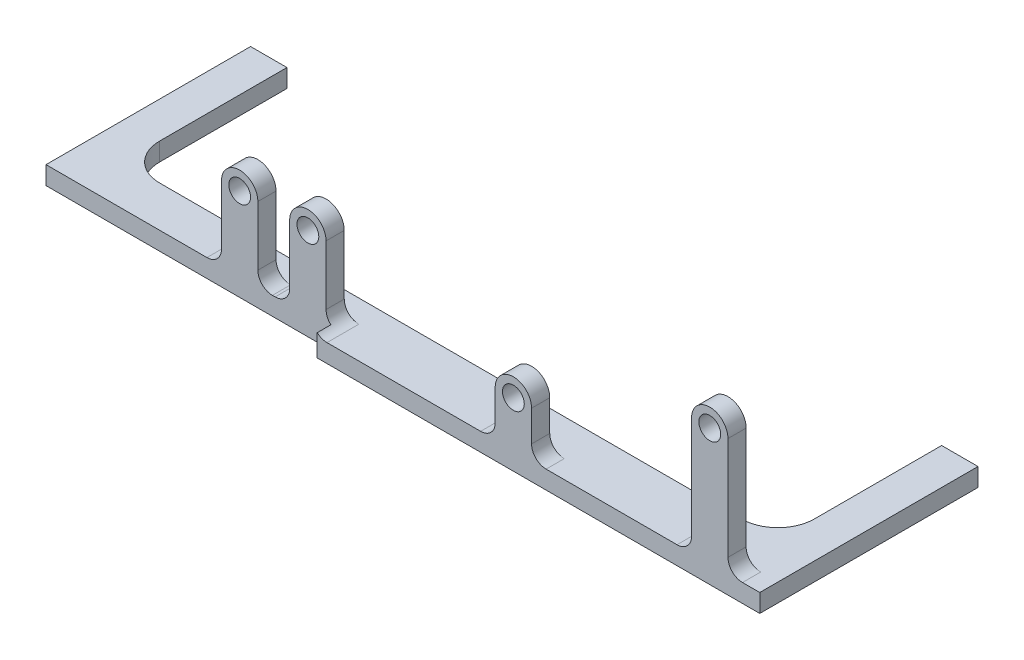
SolidWorks part; units mm, degrees
material "Alloy Steel"
ref_plane "Front Plane" through (0, 0, 0) normal (0, 0, 1) x (1, 0, 0)
ref_plane "Top Plane" through (0, 0, 0) normal (0, 1, 0) x (1, 0, 0)
ref_plane "Right Plane" through (0, 0, 0) normal (1, 0, 0) x (0, 0, -1)
sketch "Sketch1" plane through (0, 0, 0) normal (0, 1, 0) x (1, 0, 0)
  line L0 (-173.4223, 480) -> (-173.4223, 450)
  line L1 (-173.4223, 480) -> (800, 480)
  line L2 (-800, 450) -> (-800, -450)
  line L3 (-173.4223, -480) -> (800, -480)
  line L4 (800, 480) -> (800, -480)
  line L5 (0, 0) -> (800, -480) construction
  line L6 (-750, -450) -> (800, 480) construction
  line L7 (-173.4223, 450) -> (-800, 450)
  line L9 (0, 0) -> (-1738.6087, 0) construction
  line L11 (-173.4223, -450) -> (-800, -450)
  line L12 (-173.4223, -480) -> (-173.4223, -450)
  point P0 (0, 0)
  dimension "D1" = 960
  dimension "D3" = 30
extrude "Boss-Extrude1" add sketch "Sketch1" against normal blind 40
sketch "Sketch2" plane through (0, 0, 480) normal (0, 0, 1) x (1, 0, 0)
  line L0 (298, 0) -> (298, 100)
  line L1 (-173.4223, 0) -> (800, 0) construction
  line L2 (218, 0) -> (218, 100)
  line L3 (730, 0) -> (730, 258.2)
  line L4 (650, 0) -> (650, 258.2)
  line L5 (800, -40) -> (800, 0) construction
  arc A0 (218, 100) -> (298, 100) centre (258, 100) cw
  arc A1 (650, 258.2) -> (730, 258.2) centre (690, 258.2) cw
  circle A2 centre (258, 100) radius 24
  circle A3 centre (690, 258.2) radius 24
  dimension "D1" = 40
  dimension "D2" = 40
  dimension "D6" = 48
  dimension "D7" = 48
  dimension "D3" = 70
  dimension "D4" = 432
  dimension "D5" = 158.2
  dimension "D8" = 100
extrude "Boss-Extrude2" add sketch "Sketch2" against normal blind 40
sketch "Sketch3" plane through (0, 0, 450) normal (0, 0, 1) x (1, 0, 0)
  line L6 (-184, 0) -> (-184, 162.7)
  line L7 (-264, 0) -> (-264, 162.7)
  line L8 (-334, 0) -> (-334, 162.7)
  line L9 (-414, 0) -> (-414, 162.7)
  arc A4 (-264, 162.7) -> (-184, 162.7) centre (-224, 162.7) cw
  circle A5 centre (-224, 162.7) radius 24
  arc A6 (-414, 162.7) -> (-334, 162.7) centre (-374, 162.7) cw
  circle A7 centre (-374, 162.7) radius 24
  dimension "D11" = 150
  dimension "D12" = 48
  dimension "D13" = 40
mirror "Mirror1" about plane through (0, 0, 0) normal (0, 0, 1) of bodies 102
extrude "Boss-Extrude3" add sketch "Sketch3" against normal blind 40
mirror "Mirror2" about plane through (0, 0, 0) normal (0, 0, 1) of "Boss-Extrude3"
scale "Scale1" scale about centroid uniform scaling yes scale factor 0.125
fillet "Fillet3" radius 4 8 edges at (100.696, -9.9224, -57.5) (46.696, -9.9224, -57.5) (-13.554, -9.9224, -53.75) (-32.304, -9.9224, -53.75) (100.696, -9.9224, 57.5) (46.696, -9.9224, 57.5) (-13.554, -9.9224, 53.75) (-32.304, -9.9224, 53.75)
fillet "Fillet4" radius 4 8 edges at (-3.554, -9.9224, -53.75) (-22.304, -9.9224, -53.75) (56.696, -9.9224, -57.5) (110.696, -9.9224, -57.5) (110.696, -9.9224, 57.5) (56.696, -9.9224, 57.5) (-3.554, -9.9224, 53.75) (-22.304, -9.9224, 53.75)
sketch "Sketch4" plane through (0, -9.9224, 0) normal (0, 1, 0) x (1, 0, 0)
  line L0 (-70.554, 0) -> (109.446, 0) construction
  line L1 (-60.554, 45) -> (99.446, 45)
  line L2 (-70.554, 35) -> (-70.554, -35)
  line L3 (-60.554, -45) -> (99.446, -45)
  line L4 (109.446, 35) -> (109.446, -35)
  line L5 (119.446, -60) -> (119.446, 60) construction
  line L6 (-80.554, 56.25) -> (-80.554, -56.25) construction
  arc A0 (99.446, 45) -> (109.446, 35) centre (99.446, 35) cw
  arc A1 (99.446, -45) -> (109.446, -35) centre (99.446, -35) ccw
  arc A2 (-70.554, -35) -> (-60.554, -45) centre (-60.554, -35) ccw
  arc A3 (-60.554, 45) -> (-70.554, 35) centre (-60.554, 35) ccw
  point P8 (119.446, 0)
  point P9 (19.446, 0)
  point P12 (109.446, 45)
  point P17 (-70.554, -45)
  point P20 (-70.554, 45)
  dimension "D3" = 10
  dimension "D1" = 180
  dimension "D2" = 90
  dimension "D4" = 10
extrude "Cut-Extrude1" cut sketch "Sketch4" against normal through all both and the other way through all
sketch "Sketch5" plane through (0, -9.9224, 0) normal (0, 1, 0) x (1, 0, 0)
  line L0 (0, 0) -> (123.5098, 0)
  line L1 (123.5098, 0) -> (123.5098, -66.2129)
  line L2 (123.5098, -66.2129) -> (-94.641, -66.2129)
  line L3 (-94.641, -66.2129) -> (-94.641, 0)
  line L4 (-94.641, 0) -> (0, 0)
extrude "Cut-Extrude2" cut sketch "Sketch5" against normal through all both and the other way through all flip side to cut
sketch "Sketch7" plane through (0, 0, 0) normal (0, 0, -1) x (-1, 0, 0)
  line L3 (-119.446, -14.9224) -> (-109.446, -14.9224) construction
  line L4 (-119.446, -14.9224) -> (-119.446, -9.9224) construction
  line L5 (70.554, -14.9224) -> (80.554, -14.9224) construction
  circle A0 centre (-114.446, -12.4224) radius 1.5
  circle A1 centre (75.554, -12.4224) radius 1.5
  point P2 (-214.0389, -4.4123)
  point P3 (-207.1778, -12.7393)
  point P4 (-123.4658, -24.9427)
  point P5 (-114.446, -12.3992)
  point P6 (0, 0)
  point P7 (-131.6272, -0.545)
  point P10 (-114.446, -14.9224)
  point P13 (-128.7189, -13.4092)
  point P14 (-57.8796, -12.5223)
  point P15 (-16.4519, -12.9674)
  point P16 (-131.6272, -0.545)
  point P19 (-119.446, -12.4224)
  point P20 (1.8814, -12.4224)
  point P21 (32.7444, -12.4224)
  point P22 (64.2683, -12.4224)
  point P23 (74.6186, -12.4224)
  point P26 (75.554, -14.9224)
  dimension "D1" = 3
extrude "Cut-Extrude3" cut sketch "Sketch7" against normal blind 5
equation "\"2cmcm\"=4"
